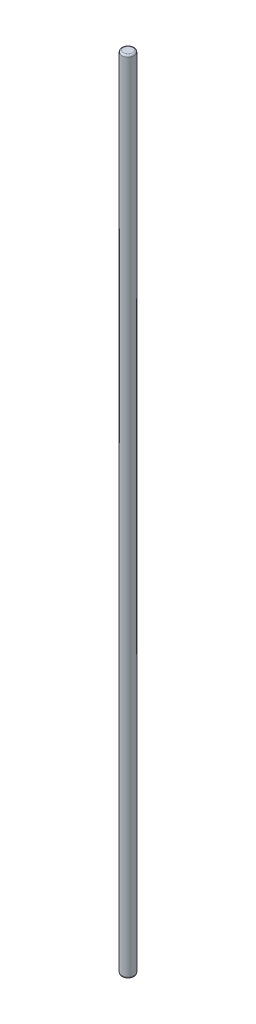
SolidWorks part; units mm, degrees
ref_plane "Front Plane" through (0, 0, 0) normal (0, 0, 1) x (1, 0, 0)
ref_plane "Top Plane" through (0, 0, 0) normal (0, 1, 0) x (1, 0, 0)
ref_plane "Right Plane" through (0, 0, 0) normal (1, 0, 0) x (0, 0, -1)
sketch "Sketch1" plane through (0, 0, 0) normal (0, 1, 0) x (1, 0, 0)
  circle A0 centre (0, 0) radius 11.25
  dimension "D1" = 22.5
extrude "Boss-Extrude1" add sketch "Sketch1" along normal blind 1450
fillet "Fillet1" radius 3 2 edges at (0, 0, 11.25) (0, 1450, 11.25)
